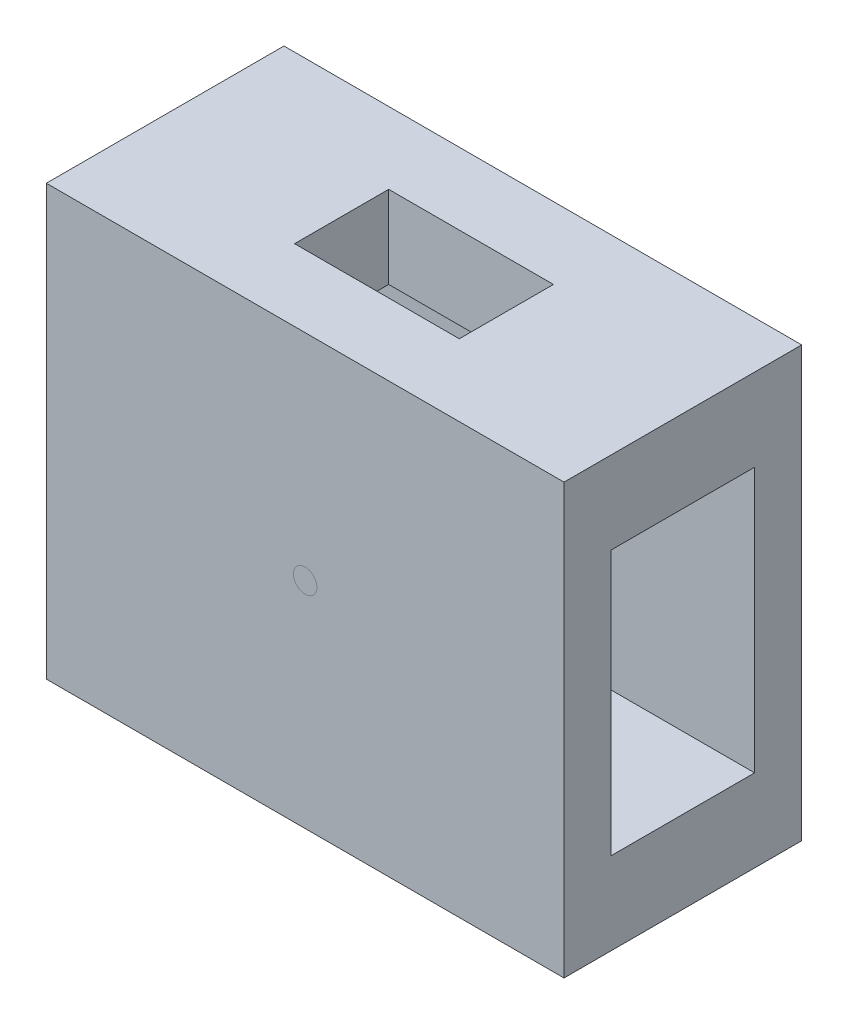
SolidWorks part; units mm, degrees
ref_plane "Front Plane" through (0, 0, 0) normal (0, 0, 1) x (1, 0, 0)
ref_plane "Top Plane" through (0, 0, 0) normal (0, 1, 0) x (1, 0, 0)
ref_plane "Right Plane" through (0, 0, 0) normal (1, 0, 0) x (0, 0, -1)
sketch "Sketch1" plane through (0, 0, 0) normal (1, 0, 0) x (0, 0, -1)
  line L1 (-10.1, -18.25) -> (10.1, -18.25)
  line L2 (-10.1, -18.25) -> (-10.1, 18.25)
  line L3 (-10.1, 18.25) -> (10.1, 18.25)
  line L4 (10.1, -18.25) -> (10.1, 18.25)
  line L7 (-6.1, -11.25) -> (6.1, -11.25)
  line L8 (-6.1, -11.25) -> (-6.1, 11.25)
  line L9 (-6.1, 11.25) -> (6.1, 11.25)
  line L10 (6.1, -11.25) -> (6.1, 11.25)
  line L11 (-6.1, -11.25) -> (6.1, 11.25) construction
  line L12 (-6.1, 11.25) -> (6.1, -11.25) construction
  point P0 (0, 0)
  point P6 (0, 0)
  dimension "D1" = 12.2
  dimension "D2" = 22.5
  dimension "D3" = 4
  dimension "D4" = 7
  dimension "D5" = 7
  dimension "D6" = 4
extrude "Boss-Extrude1" add sketch "Sketch1" along normal mid plane 44
sketch "Sketch3" plane through (0, 0, 10.1) normal (0, 0, 1) x (1, 0, 0)
  circle A0 centre (0, 0) radius 1
  dimension "D1" = 2
extrude "Cut-Extrude2" cut sketch "Sketch3" against normal blind 0.0001
sketch "Sketch6" plane through (0, 0, 0) normal (0, 1, 0) x (1, 0, 0)
  line L1 (-7, -4) -> (7, -4)
  line L2 (-7, -4) -> (-7, 4)
  line L3 (-7, 4) -> (7, 4)
  line L4 (7, -4) -> (7, 4)
  line L5 (-7, -4) -> (7, 4) construction
  line L6 (-7, 4) -> (7, -4) construction
  point P0 (0, 0)
  dimension "D1" = 14
  dimension "D2" = 8
extrude "Cut-Extrude3" cut sketch "Sketch6" against normal mid plane 50
